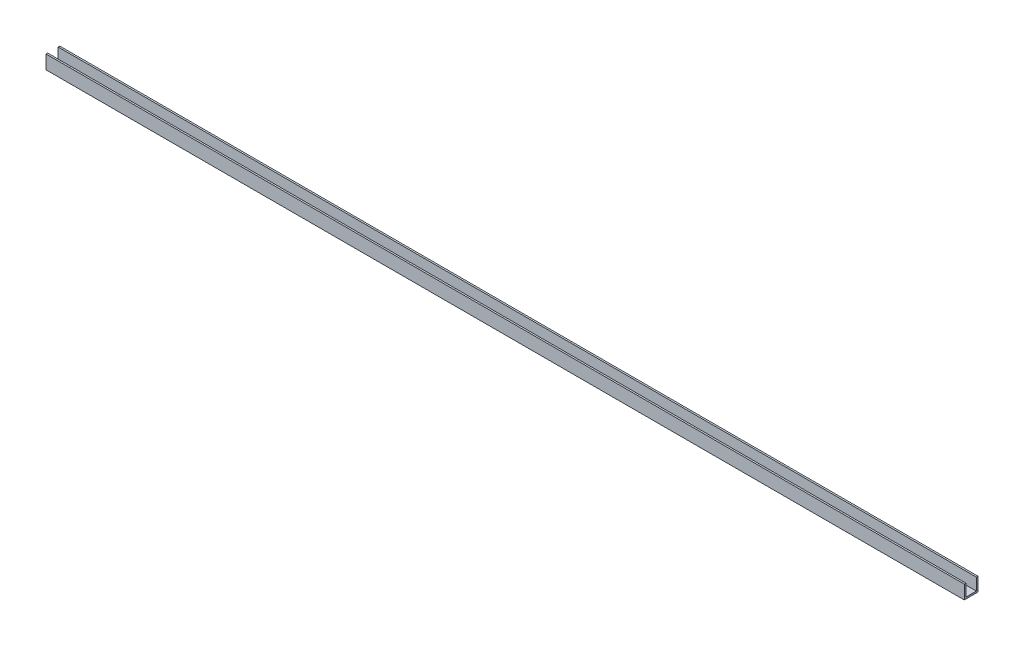
SolidWorks part; units mm, degrees
ref_plane "Front Plane" through (0, 0, 0) normal (0, 0, 1) x (1, 0, 0)
ref_plane "Top Plane" through (0, 0, 0) normal (0, 1, 0) x (1, 0, 0)
ref_plane "Right Plane" through (0, 0, 0) normal (1, 0, 0) x (0, 0, -1)
sketch "Croquis1" plane through (0, 0, 0) normal (1, 0, 0) x (0, 0, -1)
  line L0 (-6.25, -6.25) -> (-6.25, 6.25)
  line L1 (-6.25, -6.25) -> (6.25, -6.25)
  line L2 (-6.25, 6.25) -> (6.25, 6.25)
  line L3 (6.25, -6.25) -> (6.25, 6.25)
  line L4 (-6.25, -6.25) -> (6.25, 6.25) construction
  line L5 (-6.25, 6.25) -> (6.25, -6.25) construction
  line L6 (-4.75, 6.25) -> (-4.75, -4.75)
  line L7 (-4.75, -4.75) -> (4.75, -4.75)
  line L8 (4.75, -4.75) -> (4.75, 6.25)
  point P1 (0, 0)
  dimension "D1" = 12.5
  dimension "D2" = 12.5
  dimension "D3" = 1.5
extrude "Saliente-Extruir1" add sketch "Croquis1" along normal blind 835 contours L8 L7 L6 L2 L0 L1 L3
